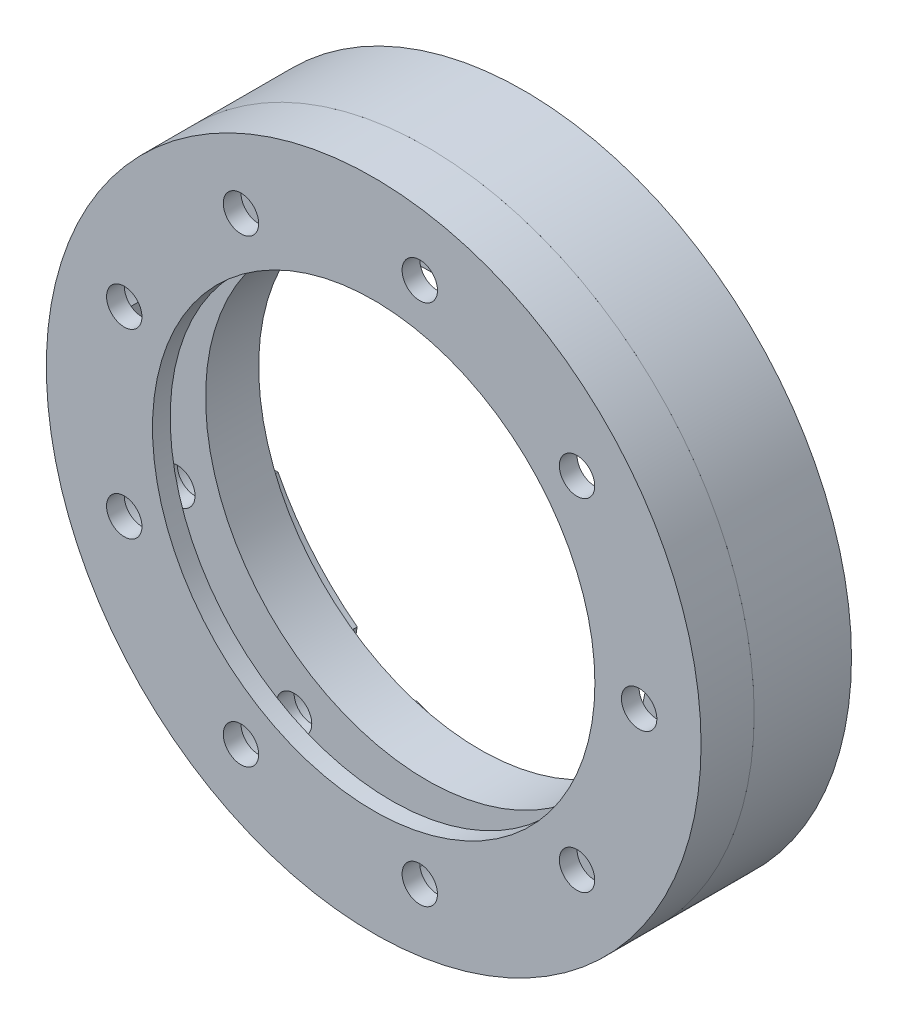
SolidWorks part; units mm, degrees
ref_plane "Front Plane" through (0, 0, 0) normal (0, 0, 1) x (1, 0, 0)
ref_plane "Top Plane" through (0, 0, 0) normal (0, 1, 0) x (1, 0, 0)
ref_plane "Right Plane" through (0, 0, 0) normal (1, 0, 0) x (0, 0, -1)
curve "Curve1"
  spline degree 3 poles (24.0011, -0.2082, 0) (23.9995, 0, 0) (24.0011, 0.2082, 0) (24.0058, 0.4158, 0) (24.0136, 0.6224, 0) (24.0244, 0.8273, 0) (24.0379, 1.0301, 0) (24.054, 1.2304, 0) (24.0724, 1.4279, 0) (24.0929, 1.6222, 0) (24.1152, 1.8132, 0) (24.139, 2.0007, 0) (24.164, 2.1846, 0) (24.1901, 2.365, 0) (24.2169, 2.5417, 0) (24.2442, 2.715, 0) (24.2718, 2.885, 0) (24.2995, 3.0517, 0) (24.3271, 3.2155, 0) (24.3545, 3.3765, 0) (24.3815, 3.5349, 0) (24.4081, 3.6909, 0) (24.4339, 3.8448, 0) (24.4591, 3.9969, 0) (24.4834, 4.1473, 0) (24.5068, 4.2962, 0) (24.5292, 4.4439, 0) (24.5506, 4.5906, 0) (24.5707, 4.7365, 0) (24.5897, 4.8817, 0) (24.6073, 5.0265, 0) (24.6236, 5.1709, 0) (24.6384, 5.3151, 0) (24.6518, 5.4593, 0) (24.6635, 5.6035, 0) (24.6736, 5.7478, 0) (24.682, 5.8924, 0) (24.6886, 6.0373, 0) (24.6934, 6.1825, 0) (24.6962, 6.3281, 0) (24.697, 6.4741, 0) (24.6958, 6.6206, 0) (24.6924, 6.7676, 0) (24.6868, 6.915, 0) (24.679, 7.0628, 0) (24.6689, 7.2111, 0) (24.6564, 7.3598, 0) (24.6415, 7.5089, 0) (24.6241, 7.6582, 0) (24.6042, 7.8078, 0) (24.5817, 7.9576, 0) (24.5566, 8.1075, 0) (24.529, 8.2575, 0) (24.4986, 8.4075, 0) (24.4656, 8.5574, 0) (24.4299, 8.7071, 0) (24.3915, 8.8565, 0) (24.3504, 9.0055, 0) (24.3065, 9.1541, 0) (24.26, 9.3022, 0) (24.2108, 9.4496, 0) (24.1589, 9.5962, 0) (24.1043, 9.742, 0) (24.0471, 9.8869, 0) (23.9874, 10.0307, 0) (23.925, 10.1735, 0) (23.8602, 10.315, 0) (23.7929, 10.4552, 0) (23.7232, 10.5941, 0) (23.6511, 10.7315, 0) (23.5768, 10.8673, 0) (23.5002, 11.0016, 0) (23.4214, 11.1342, 0) (23.3406, 11.2651, 0) (23.2577, 11.3942, 0) (23.1728, 11.5214, 0) (23.0861, 11.6468, 0) (22.9976, 11.7704, 0) (22.9073, 11.8919, 0) (22.8154, 12.0115, 0) (22.7219, 12.1292, 0) (22.6269, 12.2449, 0) (22.5304, 12.3586, 0) (22.4326, 12.4704, 0) (22.3334, 12.5802, 0) (22.2329, 12.6881, 0) (22.1313, 12.7942, 0) (22.0284, 12.8984, 0) (21.9244, 13.0009, 0) (21.8193, 13.1017, 0) (21.7131, 13.2008, 0) (21.6059, 13.2984, 0) (21.4976, 13.3945, 0) (21.3883, 13.4893, 0) (21.2779, 13.5828, 0) (21.1664, 13.6751, 0) (21.0538, 13.7665, 0) (20.94, 13.857, 0) (20.825, 13.9468, 0) (20.7087, 14.036, 0) (20.5912, 14.1249, 0) (20.4722, 14.2135, 0) (20.3517, 14.3021, 0) (20.2296, 14.3909, 0) (20.1058, 14.4801, 0) (19.9803, 14.57, 0) (19.8529, 14.6606, 0) (19.7236, 14.7524, 0) (19.5922, 14.8454, 0) (19.4588, 14.9401, 0) (19.3232, 15.0366, 0) (19.1854, 15.1352, 0) (19.0454, 15.2362, 0) (18.9033, 15.3397, 0) (18.7591, 15.4462, 0) (18.613, 15.5556, 0) (18.465, 15.6684, 0) (18.3154, 15.7846, 0) (18.1644, 15.9043, 0) (18.0124, 16.0277, 0) (17.8597, 16.1548, 0) (17.7066, 16.2855, 0) (17.5537, 16.4198, 0) (17.4013, 16.5575, 0) (17.2498, 16.6984, 0) (17.0999, 16.8422, 0) (16.9518, 16.9886, 0) (16.806, 17.1372, 0) (16.6629, 17.2876, 0) (16.5228, 17.4393, 0) (16.3859, 17.5919, 0) (16.2525, 17.7449, 0) (16.1227, 17.8979, 0) (15.9965, 18.0505, 0) (15.8741, 18.2023, 0) (15.7552, 18.3529, 0) (15.6399, 18.5021, 0) (15.528, 18.6497, 0) (15.4193, 18.7954, 0) (15.3136, 18.939, 0) (15.2107, 19.0806, 0) (15.1103, 19.22, 0) (15.0123, 19.3573, 0) (14.9163, 19.4924, 0) (14.822, 19.6253, 0) (14.7293, 19.7561, 0) (14.6379, 19.885, 0) (14.5474, 20.0119, 0) (14.4578, 20.1369, 0) (14.3687, 20.2603, 0) (14.28, 20.3819, 0) (14.1914, 20.5021, 0) (14.1027, 20.6207, 0) (14.0138, 20.7379, 0) (13.9244, 20.8539, 0) (13.8345, 20.9685, 0) (13.7437, 21.082, 0) (13.6521, 21.1944, 0) (13.5595, 21.3056, 0) (13.4657, 21.4157, 0) (13.3706, 21.5248, 0) (13.2741, 21.6328, 0) (13.1762, 21.7398, 0) (13.0766, 21.8457, 0) (12.9755, 21.9505, 0) (12.8725, 22.0542, 0) (12.7679, 22.1568, 0) (12.6613, 22.2582, 0) (12.5529, 22.3583, 0) (12.4426, 22.4572, 0) (12.3303, 22.5547, 0) (12.2161, 22.6508, 0) (12.1, 22.7455, 0) (11.9818, 22.8386, 0) (11.8617, 22.9301, 0) (11.7396, 23.0199, 0) (11.6157, 23.108, 0) (11.4898, 23.1942, 0) (11.3621, 23.2786, 0) (11.2325, 23.361, 0) (11.1012, 23.4413, 0) (10.9682, 23.5195, 0) (10.8335, 23.5956, 0) (10.6973, 23.6694, 0) (10.5595, 23.7408, 0) (10.4203, 23.81, 0) (10.2797, 23.8766, 0) (10.1379, 23.9409, 0) (9.9949, 24.0025, 0) (9.8508, 24.0617, 0) (9.7056, 24.1182, 0) (9.5596, 24.1721, 0) (9.4128, 24.2233, 0) (9.2652, 24.2719, 0) (9.117, 24.3177, 0) (8.9683, 24.3609, 0) (8.8192, 24.4013, 0) (8.6697, 24.4391, 0) (8.5199, 24.4741, 0) (8.37, 24.5064, 0) (8.22, 24.5361, 0) (8.07, 24.5632, 0) (7.9201, 24.5876, 0) (7.7704, 24.6094, 0) (7.6208, 24.6287, 0) (7.4716, 24.6454, 0) (7.3226, 24.6597, 0) (7.174, 24.6716, 0) (7.0258, 24.6812, 0) (6.8781, 24.6884, 0) (6.7308, 24.6934, 0) (6.584, 24.6963, 0) (6.4376, 24.697, 0) (6.2917, 24.6957, 0) (6.1461, 24.6924, 0) (6.001, 24.6871, 0) (5.8562, 24.6801, 0) (5.7117, 24.6713, 0) (5.5674, 24.6607, 0) (5.4232, 24.6486, 0) (5.2791, 24.6349, 0) (5.1348, 24.6197, 0) (4.9903, 24.603, 0) (4.8455, 24.585, 0) (4.7001, 24.5658, 0) (4.554, 24.5453, 0) (4.4071, 24.5237, 0) (4.2591, 24.5011, 0) (4.1098, 24.4774, 0) (3.959, 24.4529, 0) (3.8065, 24.4275, 0) (3.6521, 24.4015, 0) (3.4955, 24.3748, 0) (3.3365, 24.3477, 0) (3.1748, 24.3202, 0) (3.0103, 24.2926, 0) (2.8428, 24.2649, 0) (2.672, 24.2373, 0) (2.4979, 24.2101, 0) (2.3202, 24.1835, 0) (2.139, 24.1577, 0) (1.9542, 24.1329, 0) (1.7658, 24.1095, 0) (1.574, 24.0876, 0) (1.3788, 24.0676, 0) (1.1806, 24.0498, 0) (0.9796, 24.0343, 0) (0.7762, 24.0214, 0) (0.5709, 24.0114, 0) (0.364, 24.0043, 0) (0.1562, 24.0004, 0) (-0.0521, 23.9996, 0) (-0.2602, 24.0019, 0) (-0.4676, 24.0075, 0) (-0.6737, 24.016, 0) (-0.8782, 24.0275, 0) (-1.0804, 24.0417, 0) (-1.2801, 24.0584, 0) (-1.4768, 24.0774, 0) (-1.6703, 24.0983, 0) (-1.8604, 24.121, 0) (-2.047, 24.1451, 0) (-2.2301, 24.1705, 0) (-2.4095, 24.1967, 0) (-2.5854, 24.2237, 0) (-2.7578, 24.2511, 0) (-2.927, 24.2787, 0) (-3.093, 24.3064, 0) (-3.256, 24.334, 0) (-3.4163, 24.3613, 0) (-3.5741, 24.3882, 0) (-3.7296, 24.4146, 0) (-3.883, 24.4403, 0) (-4.0346, 24.4652, 0) (-4.1846, 24.4894, 0) (-4.3332, 24.5125, 0) (-4.4807, 24.5347, 0) (-4.6272, 24.5557, 0) (-4.7729, 24.5756, 0) (-4.918, 24.5942, 0) (-5.0626, 24.6115, 0) (-5.207, 24.6274, 0) (-5.3512, 24.6419, 0) (-5.4953, 24.6549, 0) (-5.6396, 24.6662, 0) (-5.7839, 24.6759, 0) (-5.9286, 24.6838, 0) (-6.0735, 24.69, 0) (-6.2188, 24.6943, 0) (-6.3646, 24.6966, 0) (-6.5107, 24.6969, 0) (-6.6573, 24.6951, 0) (-6.8044, 24.6912, 0) (-6.9519, 24.6851, 0) (-7.0999, 24.6767, 0) (-7.2483, 24.666, 0) (-7.397, 24.6529, 0) (-7.5462, 24.6373, 0) (-7.6956, 24.6193, 0) (-7.8452, 24.5988, 0) (-7.9951, 24.5757, 0) (-8.145, 24.55, 0) (-8.295, 24.5216, 0) (-8.445, 24.4906, 0) (-8.5948, 24.4569, 0) (-8.7444, 24.4205, 0) (-8.8938, 24.3815, 0) (-9.0427, 24.3397, 0) (-9.1912, 24.2952, 0) (-9.3391, 24.2479, 0) (-9.4863, 24.198, 0) (-9.6327, 24.1455, 0) (-9.7783, 24.0903, 0) (-9.9229, 24.0324, 0) (-10.0665, 23.972, 0) (-10.209, 23.9091, 0) (-10.3502, 23.8436, 0) (-10.4901, 23.7757, 0) (-10.6286, 23.7054, 0) (-10.7656, 23.6327, 0) (-10.9011, 23.5578, 0) (-11.0349, 23.4807, 0) (-11.1671, 23.4014, 0) (-11.2975, 23.32, 0) (-11.4262, 23.2366, 0) (-11.553, 23.1513, 0) (-11.6779, 23.0642, 0) (-11.8009, 22.9752, 0) (-11.922, 22.8845, 0) (-12.0411, 22.7922, 0) (-12.1583, 22.6983, 0) (-12.2735, 22.6029, 0) (-12.3867, 22.5061, 0) (-12.498, 22.4079, 0) (-12.6074, 22.3084, 0) (-12.7148, 22.2076, 0) (-12.8204, 22.1056, 0) (-12.9242, 22.0025, 0) (-13.0263, 21.8982, 0) (-13.1266, 21.7929, 0) (-13.2253, 21.6864, 0) (-13.3225, 21.5789, 0) (-13.4183, 21.4704, 0) (-13.5127, 21.3608, 0) (-13.606, 21.2501, 0) (-13.6981, 21.1383, 0) (-13.7892, 21.0254, 0) (-13.8795, 20.9113, 0) (-13.9692, 20.7961, 0) (-14.0583, 20.6795, 0) (-14.1471, 20.5615, 0) (-14.2357, 20.4422, 0) (-14.3243, 20.3213, 0) (-14.4132, 20.1988, 0) (-14.5025, 20.0746, 0) (-14.5925, 19.9487, 0) (-14.6834, 19.8208, 0) (-14.7755, 19.691, 0) (-14.8689, 19.5591, 0) (-14.964, 19.4251, 0) (-15.061, 19.2889, 0) (-15.1602, 19.1506, 0) (-15.2618, 19.0101, 0) (-15.3661, 18.8675, 0) (-15.4732, 18.7228, 0) (-15.5835, 18.5761, 0) (-15.6971, 18.4277, 0) (-15.8142, 18.2778, 0) (-15.9348, 18.1265, 0) (-16.0591, 17.9743, 0) (-16.1871, 17.8214, 0) (-16.3188, 17.6684, 0) (-16.4539, 17.5155, 0) (-16.5925, 17.3633, 0) (-16.7341, 17.2122, 0) (-16.8786, 17.0627, 0) (-17.0256, 16.9151, 0) (-17.1747, 16.77, 0) (-17.3254, 16.6276, 0) (-17.4774, 16.4883, 0) (-17.6301, 16.3522, 0) (-17.7832, 16.2197, 0) (-17.9361, 16.0908, 0) (-18.0885, 15.9656, 0) (-18.24, 15.844, 0) (-18.3904, 15.7261, 0) (-18.5392, 15.6116, 0) (-18.6863, 15.5005, 0) (-18.8315, 15.3926, 0) (-18.9746, 15.2876, 0) (-19.1157, 15.1854, 0) (-19.2546, 15.0856, 0) (-19.3913, 14.9881, 0) (-19.5258, 14.8926, 0) (-19.6582, 14.7987, 0) (-19.7885, 14.7063, 0) (-19.9169, 14.6152, 0) (-20.0433, 14.525, 0) (-20.1679, 14.4355, 0) (-20.2908, 14.3465, 0) (-20.4121, 14.2578, 0) (-20.5318, 14.1692, 0) (-20.6501, 14.0805, 0) (-20.767, 13.9915, 0) (-20.8826, 13.902, 0) (-20.997, 13.8119, 0) (-21.1102, 13.7209, 0) (-21.2223, 13.6291, 0) (-21.3332, 13.5362, 0) (-21.4431, 13.4421, 0) (-21.5519, 13.3466, 0) (-21.6597, 13.2498, 0) (-21.7664, 13.1514, 0) (-21.872, 13.0515, 0) (-21.9765, 12.9499, 0) (-22.08, 12.8465, 0) (-22.1822, 12.7414, 0) (-22.2833, 12.6344, 0) (-22.3831, 12.5255, 0) (-22.4817, 12.4147, 0) (-22.5789, 12.302, 0) (-22.6746, 12.1873, 0) (-22.7689, 12.0706, 0) (-22.8616, 11.952, 0) (-22.9527, 11.8314, 0) (-23.0421, 11.7088, 0) (-23.1297, 11.5844, 0) (-23.2155, 11.458, 0) (-23.2994, 11.3299, 0) (-23.3812, 11.1999, 0) (-23.461, 11.0681, 0) (-23.5387, 10.9347, 0) (-23.6142, 10.7996, 0) (-23.6874, 10.663, 0) (-23.7583, 10.5248, 0) (-23.8268, 10.3853, 0) (-23.8929, 10.2444, 0) (-23.9565, 10.1022, 0) (-24.0176, 9.9589, 0) (-24.076, 9.8146, 0) (-24.1319, 9.6692, 0) (-24.1851, 9.523, 0) (-24.2357, 9.3759, 0) (-24.2836, 9.2282, 0) (-24.3288, 9.0799, 0) (-24.3713, 8.9311, 0) (-24.411, 8.7818, 0) (-24.4481, 8.6322, 0) (-24.4824, 8.4825, 0) (-24.5141, 8.3325, 0) (-24.5431, 8.1825, 0) (-24.5695, 8.0326, 0) (-24.5933, 7.8827, 0) (-24.6144, 7.733, 0) (-24.6331, 7.5835, 0) (-24.6492, 7.4343, 0) (-24.6629, 7.2854, 0) (-24.6742, 7.1369, 0) (-24.6832, 6.9889, 0) (-24.6899, 6.8412, 0) (-24.6943, 6.6941, 0) (-24.6966, 6.5473, 0) (-24.6968, 6.4011, 0) (-24.695, 6.2552, 0) (-24.6912, 6.1098, 0) (-24.6855, 5.9648, 0) (-24.678, 5.8201, 0) (-24.6688, 5.6756, 0) (-24.6579, 5.5314, 0) (-24.6453, 5.3872, 0) (-24.6312, 5.243, 0) (-24.6156, 5.0987, 0) (-24.5987, 4.9542, 0) (-24.5804, 4.8092, 0) (-24.5608, 4.6637, 0) (-24.54, 4.5174, 0) (-24.5182, 4.3702, 0) (-24.4952, 4.2219, 0) (-24.4714, 4.0723, 0) (-24.4466, 3.9211, 0) (-24.4211, 3.7681, 0) (-24.3949, 3.6132, 0) (-24.3681, 3.456, 0) (-24.3409, 3.2963, 0) (-24.3133, 3.134, 0) (-24.2857, 2.9687, 0) (-24.258, 2.8004, 0) (-24.2305, 2.6288, 0) (-24.2034, 2.4538, 0) (-24.177, 2.2752, 0) (-24.1514, 2.0931, 0) (-24.1269, 1.9074, 0) (-24.1038, 1.7182, 0) (-24.0824, 1.5255, 0) (-24.0629, 1.3295, 0) (-24.0457, 1.1306, 0) (-24.0308, 0.929, 0) (-24.0187, 0.725, 0) (-24.0093, 0.5193, 0) (-24.003, 0.3121, 0) (-23.9999, 0.1041, 0) (-23.9999, -0.1041, 0) (-24.003, -0.3121, 0) (-24.0093, -0.5193, 0) (-24.0187, -0.725, 0) (-24.0308, -0.929, 0) (-24.0457, -1.1306, 0) (-24.0629, -1.3295, 0) (-24.0824, -1.5255, 0) (-24.1038, -1.7182, 0) (-24.1269, -1.9074, 0) (-24.1514, -2.0931, 0) (-24.177, -2.2752, 0) (-24.2034, -2.4538, 0) (-24.2305, -2.6288, 0) (-24.258, -2.8004, 0) (-24.2857, -2.9687, 0) (-24.3133, -3.134, 0) (-24.3409, -3.2963, 0) (-24.3681, -3.456, 0) (-24.3949, -3.6132, 0) (-24.4211, -3.7681, 0) (-24.4466, -3.9211, 0) (-24.4714, -4.0723, 0) (-24.4952, -4.2219, 0) (-24.5182, -4.3702, 0) (-24.54, -4.5174, 0) (-24.5608, -4.6637, 0) (-24.5804, -4.8092, 0) (-24.5987, -4.9542, 0) (-24.6156, -5.0987, 0) (-24.6312, -5.243, 0) (-24.6453, -5.3872, 0) (-24.6579, -5.5314, 0) (-24.6688, -5.6756, 0) (-24.678, -5.8201, 0) (-24.6855, -5.9648, 0) (-24.6912, -6.1098, 0) (-24.695, -6.2552, 0) (-24.6968, -6.4011, 0) (-24.6966, -6.5473, 0) (-24.6943, -6.6941, 0) (-24.6899, -6.8412, 0) (-24.6832, -6.9889, 0) (-24.6742, -7.1369, 0) (-24.6629, -7.2854, 0) (-24.6492, -7.4343, 0) (-24.6331, -7.5835, 0) (-24.6144, -7.733, 0) (-24.5933, -7.8827, 0) (-24.5695, -8.0326, 0) (-24.5431, -8.1825, 0) (-24.5141, -8.3325, 0) (-24.4824, -8.4825, 0) (-24.4481, -8.6322, 0) (-24.411, -8.7818, 0) (-24.3713, -8.9311, 0) (-24.3288, -9.0799, 0) (-24.2836, -9.2282, 0) (-24.2357, -9.3759, 0) (-24.1851, -9.523, 0) (-24.1319, -9.6692, 0) (-24.076, -9.8146, 0) (-24.0176, -9.9589, 0) (-23.9565, -10.1022, 0) (-23.8929, -10.2444, 0) (-23.8268, -10.3853, 0) (-23.7583, -10.5248, 0) (-23.6874, -10.663, 0) (-23.6142, -10.7996, 0) (-23.5387, -10.9347, 0) (-23.461, -11.0681, 0) (-23.3812, -11.1999, 0) (-23.2994, -11.3299, 0) (-23.2155, -11.458, 0) (-23.1297, -11.5844, 0) (-23.0421, -11.7088, 0) (-22.9527, -11.8314, 0) (-22.8616, -11.952, 0) (-22.7689, -12.0706, 0) (-22.6746, -12.1873, 0) (-22.5789, -12.302, 0) (-22.4817, -12.4147, 0) (-22.3831, -12.5255, 0) (-22.2833, -12.6344, 0) (-22.1822, -12.7414, 0) (-22.08, -12.8465, 0) (-21.9765, -12.9499, 0) (-21.872, -13.0515, 0) (-21.7664, -13.1514, 0) (-21.6597, -13.2498, 0) (-21.5519, -13.3466, 0) (-21.4431, -13.4421, 0) (-21.3332, -13.5362, 0) (-21.2223, -13.6291, 0) (-21.1102, -13.7209, 0) (-20.997, -13.8119, 0) (-20.8826, -13.902, 0) (-20.767, -13.9915, 0) (-20.6501, -14.0805, 0) (-20.5318, -14.1692, 0) (-20.4121, -14.2578, 0) (-20.2908, -14.3465, 0) (-20.1679, -14.4355, 0) (-20.0433, -14.525, 0) (-19.9169, -14.6152, 0) (-19.7885, -14.7063, 0) (-19.6582, -14.7987, 0) (-19.5258, -14.8926, 0) (-19.3913, -14.9881, 0) (-19.2546, -15.0856, 0) (-19.1157, -15.1854, 0) (-18.9746, -15.2876, 0) (-18.8315, -15.3926, 0) (-18.6863, -15.5005, 0) (-18.5392, -15.6116, 0) (-18.3904, -15.7261, 0) (-18.24, -15.844, 0) (-18.0885, -15.9656, 0) (-17.9361, -16.0908, 0) (-17.7832, -16.2197, 0) (-17.6301, -16.3522, 0) (-17.4774, -16.4883, 0) (-17.3254, -16.6276, 0) (-17.1747, -16.77, 0) (-17.0256, -16.9151, 0) (-16.8786, -17.0627, 0) (-16.7341, -17.2122, 0) (-16.5925, -17.3633, 0) (-16.4539, -17.5155, 0) (-16.3188, -17.6684, 0) (-16.1871, -17.8214, 0) (-16.0591, -17.9743, 0) (-15.9348, -18.1265, 0) (-15.8142, -18.2778, 0) (-15.6971, -18.4277, 0) (-15.5835, -18.5761, 0) (-15.4732, -18.7228, 0) (-15.3661, -18.8675, 0) (-15.2618, -19.0101, 0) (-15.1602, -19.1506, 0) (-15.061, -19.2889, 0) (-14.964, -19.4251, 0) (-14.8689, -19.5591, 0) (-14.7755, -19.691, 0) (-14.6834, -19.8208, 0) (-14.5925, -19.9487, 0) (-14.5025, -20.0746, 0) (-14.4132, -20.1988, 0) (-14.3243, -20.3213, 0) (-14.2357, -20.4422, 0) (-14.1471, -20.5615, 0) (-14.0583, -20.6795, 0) (-13.9692, -20.7961, 0) (-13.8795, -20.9113, 0) (-13.7892, -21.0254, 0) (-13.6981, -21.1383, 0) (-13.606, -21.2501, 0) (-13.5127, -21.3608, 0) (-13.4183, -21.4704, 0) (-13.3225, -21.5789, 0) (-13.2253, -21.6864, 0) (-13.1266, -21.7929, 0) (-13.0263, -21.8982, 0) (-12.9242, -22.0025, 0) (-12.8204, -22.1056, 0) (-12.7148, -22.2076, 0) (-12.6074, -22.3084, 0) (-12.498, -22.4079, 0) (-12.3867, -22.5061, 0) (-12.2735, -22.6029, 0) (-12.1583, -22.6983, 0) (-12.0411, -22.7922, 0) (-11.922, -22.8845, 0) (-11.8009, -22.9752, 0) (-11.6779, -23.0642, 0) (-11.553, -23.1513, 0) (-11.4262, -23.2366, 0) (-11.2975, -23.32, 0) (-11.1671, -23.4014, 0) (-11.0349, -23.4807, 0) (-10.9011, -23.5578, 0) (-10.7656, -23.6327, 0) (-10.6286, -23.7054, 0) (-10.4901, -23.7757, 0) (-10.3502, -23.8436, 0) (-10.209, -23.9091, 0) (-10.0665, -23.972, 0) (-9.9229, -24.0324, 0) (-9.7783, -24.0903, 0) (-9.6327, -24.1455, 0) (-9.4863, -24.198, 0) (-9.3391, -24.2479, 0) (-9.1912, -24.2952, 0) (-9.0427, -24.3397, 0) (-8.8938, -24.3815, 0) (-8.7444, -24.4205, 0) (-8.5948, -24.4569, 0) (-8.445, -24.4906, 0) (-8.295, -24.5216, 0) (-8.145, -24.55, 0) (-7.9951, -24.5757, 0) (-7.8452, -24.5988, 0) (-7.6956, -24.6193, 0) (-7.5462, -24.6373, 0) (-7.397, -24.6529, 0) (-7.2483, -24.666, 0) (-7.0999, -24.6767, 0) (-6.9519, -24.6851, 0) (-6.8044, -24.6912, 0) (-6.6573, -24.6951, 0) (-6.5107, -24.6969, 0) (-6.3646, -24.6966, 0) (-6.2188, -24.6943, 0) (-6.0735, -24.69, 0) (-5.9286, -24.6838, 0) (-5.7839, -24.6759, 0) (-5.6396, -24.6662, 0) (-5.4953, -24.6549, 0) (-5.3512, -24.6419, 0) (-5.207, -24.6274, 0) (-5.0626, -24.6115, 0) (-4.918, -24.5942, 0) (-4.7729, -24.5756, 0) (-4.6272, -24.5557, 0) (-4.4807, -24.5347, 0) (-4.3332, -24.5125, 0) (-4.1846, -24.4894, 0) (-4.0346, -24.4652, 0) (-3.883, -24.4403, 0) (-3.7296, -24.4146, 0) (-3.5741, -24.3882, 0) (-3.4163, -24.3613, 0) (-3.256, -24.334, 0) (-3.093, -24.3064, 0) (-2.927, -24.2787, 0) (-2.7578, -24.2511, 0) (-2.5854, -24.2237, 0) (-2.4095, -24.1967, 0) (-2.2301, -24.1705, 0) (-2.047, -24.1451, 0) (-1.8604, -24.121, 0) (-1.6703, -24.0983, 0) (-1.4768, -24.0774, 0) (-1.2801, -24.0584, 0) (-1.0804, -24.0417, 0) (-0.8782, -24.0275, 0) (-0.6737, -24.016, 0) (-0.4676, -24.0075, 0) (-0.2602, -24.0019, 0) (-0.0521, -23.9996, 0) (0.1562, -24.0004, 0) (0.364, -24.0043, 0) (0.5709, -24.0114, 0) (0.7762, -24.0214, 0) (0.9796, -24.0343, 0) (1.1806, -24.0498, 0) (1.3788, -24.0676, 0) (1.574, -24.0876, 0) (1.7658, -24.1095, 0) (1.9542, -24.1329, 0) (2.139, -24.1577, 0) (2.3202, -24.1835, 0) (2.4979, -24.2101, 0) (2.672, -24.2373, 0) (2.8428, -24.2649, 0) (3.0103, -24.2926, 0) (3.1748, -24.3202, 0) (3.3365, -24.3477, 0) (3.4955, -24.3748, 0) (3.6521, -24.4015, 0) (3.8065, -24.4275, 0) (3.959, -24.4529, 0) (4.1098, -24.4774, 0) (4.2591, -24.5011, 0) (4.4071, -24.5237, 0) (4.554, -24.5453, 0) (4.7001, -24.5658, 0) (4.8455, -24.585, 0) (4.9903, -24.603, 0) (5.1348, -24.6197, 0) (5.2791, -24.6349, 0) (5.4232, -24.6486, 0) (5.5674, -24.6607, 0) (5.7117, -24.6713, 0) (5.8562, -24.6801, 0) (6.001, -24.6871, 0) (6.1461, -24.6924, 0) (6.2917, -24.6957, 0) (6.4376, -24.697, 0) (6.584, -24.6963, 0) (6.7308, -24.6934, 0) (6.8781, -24.6884, 0) (7.0258, -24.6812, 0) (7.174, -24.6716, 0) (7.3226, -24.6597, 0) (7.4716, -24.6454, 0) (7.6208, -24.6287, 0) (7.7704, -24.6094, 0) (7.9201, -24.5876, 0) (8.07, -24.5632, 0) (8.22, -24.5361, 0) (8.37, -24.5064, 0) (8.5199, -24.4741, 0) (8.6697, -24.4391, 0) (8.8192, -24.4013, 0) (8.9683, -24.3609, 0) (9.117, -24.3177, 0) (9.2652, -24.2719, 0) (9.4128, -24.2233, 0) (9.5596, -24.1721, 0) (9.7056, -24.1182, 0) (9.8508, -24.0617, 0) (9.9949, -24.0025, 0) (10.1379, -23.9409, 0) (10.2797, -23.8766, 0) (10.4203, -23.81, 0) (10.5595, -23.7408, 0) (10.6973, -23.6694, 0) (10.8335, -23.5956, 0) (10.9682, -23.5195, 0) (11.1012, -23.4413, 0) (11.2325, -23.361, 0) (11.3621, -23.2786, 0) (11.4898, -23.1942, 0) (11.6157, -23.108, 0) (11.7396, -23.0199, 0) (11.8617, -22.9301, 0) (11.9818, -22.8386, 0) (12.1, -22.7455, 0) (12.2161, -22.6508, 0) (12.3303, -22.5547, 0) (12.4426, -22.4572, 0) (12.5529, -22.3583, 0) (12.6613, -22.2582, 0) (12.7679, -22.1568, 0) (12.8725, -22.0542, 0) (12.9755, -21.9505, 0) (13.0766, -21.8457, 0) (13.1762, -21.7398, 0) (13.2741, -21.6328, 0) (13.3706, -21.5248, 0) (13.4657, -21.4157, 0) (13.5595, -21.3056, 0) (13.6521, -21.1944, 0) (13.7437, -21.082, 0) (13.8345, -20.9685, 0) (13.9244, -20.8539, 0) (14.0138, -20.7379, 0) (14.1027, -20.6207, 0) (14.1914, -20.5021, 0) (14.28, -20.3819, 0) (14.3687, -20.2603, 0) (14.4578, -20.1369, 0) (14.5474, -20.0119, 0) (14.6379, -19.885, 0) (14.7293, -19.7561, 0) (14.822, -19.6253, 0) (14.9163, -19.4924, 0) (15.0123, -19.3573, 0) (15.1103, -19.22, 0) (15.2107, -19.0806, 0) (15.3136, -18.939, 0) (15.4193, -18.7954, 0) (15.528, -18.6497, 0) (15.6399, -18.5021, 0) (15.7552, -18.3529, 0) (15.8741, -18.2023, 0) (15.9965, -18.0505, 0) (16.1227, -17.8979, 0) (16.2525, -17.7449, 0) (16.3859, -17.5919, 0) (16.5228, -17.4393, 0) (16.6629, -17.2876, 0) (16.806, -17.1372, 0) (16.9518, -16.9886, 0) (17.0999, -16.8422, 0) (17.2498, -16.6984, 0) (17.4013, -16.5575, 0) (17.5537, -16.4198, 0) (17.7066, -16.2855, 0) (17.8597, -16.1548, 0) (18.0124, -16.0277, 0) (18.1644, -15.9043, 0) (18.3154, -15.7846, 0) (18.465, -15.6684, 0) (18.613, -15.5556, 0) (18.7591, -15.4462, 0) (18.9033, -15.3397, 0) (19.0454, -15.2362, 0) (19.1854, -15.1352, 0) (19.3232, -15.0366, 0) (19.4588, -14.9401, 0) (19.5922, -14.8454, 0) (19.7236, -14.7524, 0) (19.8529, -14.6606, 0) (19.9803, -14.57, 0) (20.1058, -14.4801, 0) (20.2296, -14.3909, 0) (20.3517, -14.3021, 0) (20.4722, -14.2135, 0) (20.5912, -14.1249, 0) (20.7087, -14.036, 0) (20.825, -13.9468, 0) (20.94, -13.857, 0) (21.0538, -13.7665, 0) (21.1664, -13.6751, 0) (21.2779, -13.5828, 0) (21.3883, -13.4893, 0) (21.4976, -13.3945, 0) (21.6059, -13.2984, 0) (21.7131, -13.2008, 0) (21.8193, -13.1017, 0) (21.9244, -13.0009, 0) (22.0284, -12.8984, 0) (22.1313, -12.7942, 0) (22.2329, -12.6881, 0) (22.3334, -12.5802, 0) (22.4326, -12.4704, 0) (22.5304, -12.3586, 0) (22.6269, -12.2449, 0) (22.7219, -12.1292, 0) (22.8154, -12.0115, 0) (22.9073, -11.8919, 0) (22.9976, -11.7704, 0) (23.0861, -11.6468, 0) (23.1728, -11.5214, 0) (23.2577, -11.3942, 0) (23.3406, -11.2651, 0) (23.4214, -11.1342, 0) (23.5002, -11.0016, 0) (23.5768, -10.8673, 0) (23.6511, -10.7315, 0) (23.7232, -10.5941, 0) (23.7929, -10.4552, 0) (23.8602, -10.315, 0) (23.925, -10.1735, 0) (23.9874, -10.0307, 0) (24.0471, -9.8869, 0) (24.1043, -9.742, 0) (24.1589, -9.5962, 0) (24.2108, -9.4496, 0) (24.26, -9.3022, 0) (24.3065, -9.1541, 0) (24.3504, -9.0055, 0) (24.3915, -8.8565, 0) (24.4299, -8.7071, 0) (24.4656, -8.5574, 0) (24.4986, -8.4075, 0) (24.529, -8.2575, 0) (24.5566, -8.1075, 0) (24.5817, -7.9576, 0) (24.6042, -7.8078, 0) (24.6241, -7.6582, 0) (24.6415, -7.5089, 0) (24.6564, -7.3598, 0) (24.6689, -7.2111, 0) (24.679, -7.0628, 0) (24.6868, -6.915, 0) (24.6924, -6.7676, 0) (24.6958, -6.6206, 0) (24.697, -6.4741, 0) (24.6962, -6.3281, 0) (24.6934, -6.1825, 0) (24.6886, -6.0373, 0) (24.682, -5.8924, 0) (24.6736, -5.7478, 0) (24.6635, -5.6035, 0) (24.6518, -5.4593, 0) (24.6384, -5.3151, 0) (24.6236, -5.1709, 0) (24.6073, -5.0265, 0) (24.5897, -4.8817, 0) (24.5707, -4.7365, 0) (24.5506, -4.5906, 0) (24.5292, -4.4439, 0) (24.5068, -4.2962, 0) (24.4834, -4.1473, 0) (24.4591, -3.9969, 0) (24.4339, -3.8448, 0) (24.4081, -3.6909, 0) (24.3815, -3.5349, 0) (24.3545, -3.3765, 0) (24.3271, -3.2155, 0) (24.2995, -3.0517, 0) (24.2718, -2.885, 0) (24.2442, -2.715, 0) (24.2169, -2.5417, 0) (24.1901, -2.365, 0) (24.164, -2.1846, 0) (24.139, -2.0007, 0) (24.1152, -1.8132, 0) (24.0929, -1.6222, 0) (24.0724, -1.4279, 0) (24.054, -1.2304, 0) (24.0379, -1.0301, 0) (24.0244, -0.8273, 0) (24.0136, -0.6224, 0) (24.0058, -0.4158, 0) (24.0011, -0.2082, 0) (23.9995, 0, 0) (24.0011, 0.2082, 0) knots -0.003862 -0.00258 -0.001291 0 0.001291 0.00258 0.003862 0.005134 0.006395 0.007641 0.008871 0.010083 0.011275 0.012446 0.013597 0.014726 0.015834 0.016921 0.017988 0.019035 0.020064 0.021076 0.022071 0.023052 0.024019 0.024974 0.025917 0.026851 0.027777 0.028696 0.029608 0.030515 0.031419 0.032319 0.033217 0.034114 0.035011 0.035908 0.036805 0.037703 0.038604 0.039506 0.040411 0.041319 0.04223 0.043144 0.044062 0.044983 0.045908 0.046836 0.047768 0.048703 0.049642 0.050585 0.05153 0.052478 0.053429 0.054383 0.055339 0.056298 0.057258 0.05822 0.059183 0.060147 0.061112 0.062078 0.063043 0.064008 0.064973 0.065937 0.0669 0.067862 0.068822 0.06978 0.070736 0.07169 0.07264 0.073588 0.074533 0.075475 0.076414 0.077349 0.07828 0.079208 0.080132 0.081053 0.08197 0.082884 0.083794 0.084702 0.085607 0.086509 0.087409 0.088307 0.089205 0.090101 0.090998 0.091895 0.092793 0.093694 0.094598 0.095506 0.096419 0.097338 0.098265 0.0992 0.100145 0.101101 0.10207 0.103052 0.10405 0.105063 0.106095 0.107144 0.108214 0.109303 0.110414 0.111546 0.112699 0.113873 0.115068 0.116282 0.117514 0.118762 0.120024 0.121298 0.122581 0.12387 0.125161 0.126453 0.12774 0.129021 0.130292 0.131551 0.132796 0.134023 0.135233 0.136422 0.137591 0.138739 0.139865 0.140971 0.142055 0.14312 0.144165 0.145192 0.146201 0.147195 0.148174 0.149139 0.150092 0.151035 0.151968 0.152892 0.15381 0.154722 0.155628 0.156531 0.157431 0.15833 0.159227 0.160123 0.16102 0.161917 0.162816 0.163717 0.164619 0.165525 0.166433 0.167344 0.168259 0.169177 0.170099 0.171024 0.171953 0.172885 0.173821 0.17476 0.175703 0.176648 0.177597 0.178549 0.179503 0.180459 0.181418 0.182378 0.18334 0.184304 0.185268 0.186233 0.187198 0.188164 0.189129 0.190094 0.191058 0.192021 0.192982 0.193942 0.1949 0.195855 0.196809 0.197759 0.198707 0.199651 0.200593 0.201531 0.202465 0.203396 0.204324 0.205247 0.206168 0.207084 0.207998 0.208908 0.209815 0.210719 0.211621 0.212521 0.21342 0.214317 0.215213 0.21611 0.217007 0.217906 0.218807 0.219711 0.22062 0.221533 0.222454 0.223381 0.224318 0.225264 0.226222 0.227192 0.228176 0.229175 0.230191 0.231225 0.232277 0.233349 0.234441 0.235554 0.236689 0.237845 0.239022 0.240219 0.241435 0.242669 0.243919 0.245183 0.246458 0.247742 0.249031 0.250323 0.251614 0.252901 0.254181 0.255451 0.256708 0.25795 0.259176 0.260382 0.261569 0.262736 0.263881 0.265005 0.266108 0.26719 0.268252 0.269294 0.270319 0.271326 0.272318 0.273295 0.274259 0.275211 0.276152 0.277084 0.278007 0.278924 0.279835 0.280741 0.281644 0.282544 0.283442 0.284339 0.285235 0.286132 0.287029 0.287928 0.288829 0.289732 0.290638 0.291547 0.292458 0.293374 0.294292 0.295214 0.29614 0.297069 0.298002 0.298938 0.299878 0.300821 0.301767 0.302716 0.303668 0.304622 0.305579 0.306538 0.307498 0.308461 0.309424 0.310388 0.311354 0.312319 0.313284 0.31425 0.315214 0.316178 0.317141 0.318102 0.319062 0.320019 0.320975 0.321928 0.322878 0.323825 0.324769 0.32571 0.326648 0.327582 0.328512 0.329439 0.330363 0.331282 0.332199 0.333112 0.334021 0.334928 0.335832 0.336734 0.337634 0.338532 0.339429 0.340325 0.341222 0.342119 0.343018 0.34392 0.344825 0.345734 0.346648 0.347569 0.348498 0.349435 0.350383 0.351342 0.352314 0.3533 0.354302 0.355319 0.356355 0.35741 0.358484 0.359579 0.360695 0.361832 0.362991 0.36417 0.36537 0.366588 0.367824 0.369076 0.370342 0.371618 0.372903 0.374193 0.375484 0.376775 0.378061 0.37934 0.380608 0.381864 0.383104 0.384327 0.385532 0.386716 0.38788 0.389023 0.390144 0.391244 0.392323 0.393383 0.394423 0.395446 0.396451 0.397441 0.398416 0.399378 0.400329 0.401269 0.402199 0.403122 0.404038 0.404949 0.405854 0.406757 0.407656 0.408554 0.409451 0.410347 0.411244 0.412142 0.413041 0.413942 0.414845 0.415752 0.416661 0.417573 0.418488 0.419407 0.42033 0.421256 0.422185 0.423118 0.424055 0.424995 0.425939 0.426885 0.427835 0.428787 0.429742 0.430699 0.431658 0.432619 0.433581 0.434545 0.435509 0.436474 0.43744 0.438405 0.43937 0.440335 0.441299 0.442261 0.443222 0.444182 0.445139 0.446094 0.447047 0.447996 0.448943 0.449887 0.450828 0.451765 0.452698 0.453628 0.454555 0.455478 0.456397 0.457313 0.458226 0.459135 0.460041 0.460945 0.461847 0.462746 0.463644 0.464541 0.465437 0.466334 0.467232 0.468131 0.469033 0.469938 0.470848 0.471763 0.472685 0.473614 0.474553 0.475502 0.476463 0.477437 0.478424 0.479428 0.480448 0.481486 0.482543 0.48362 0.484718 0.485836 0.486976 0.488137 0.489319 0.490521 0.491742 0.49298 0.494234 0.495501 0.496778 0.498064 0.499354 0.500646 0.501936 0.503222 0.504499 0.505766 0.50702 0.508258 0.509479 0.510681 0.511863 0.513024 0.514164 0.515282 0.51638 0.517457 0.518514 0.519552 0.520572 0.521576 0.522563 0.523537 0.524498 0.525447 0.526386 0.527315 0.528237 0.529152 0.530062 0.530967 0.531869 0.532768 0.533666 0.534563 0.535459 0.536356 0.537254 0.538153 0.539055 0.539959 0.540865 0.541774 0.542687 0.543603 0.544522 0.545445 0.546372 0.547302 0.548235 0.549172 0.550113 0.551057 0.552004 0.552953 0.553906 0.554861 0.555818 0.556778 0.557739 0.558701 0.559665 0.56063 0.561595 0.56256 0.563526 0.564491 0.565455 0.566419 0.567381 0.568342 0.569301 0.570258 0.571213 0.572165 0.573115 0.574061 0.575005 0.575945 0.576882 0.577815 0.578744 0.57967 0.580593 0.581512 0.582427 0.583339 0.584248 0.585155 0.586058 0.586959 0.587858 0.588756 0.589653 0.590549 0.591446 0.592344 0.593243 0.594146 0.595051 0.595962 0.596878 0.597801 0.598731 0.599671 0.600622 0.601584 0.602559 0.603549 0.604554 0.605577 0.606617 0.607677 0.608756 0.609856 0.610977 0.61212 0.613284 0.614468 0.615673 0.616896 0.618136 0.619392 0.62066 0.621939 0.623225 0.624516 0.625807 0.627097 0.628382 0.629658 0.630924 0.632176 0.633412 0.63463 0.63583 0.637009 0.638168 0.639305 0.640421 0.641516 0.64259 0.643645 0.644681 0.645698 0.6467 0.647686 0.648658 0.649617 0.650565 0.651502 0.652431 0.653352 0.654266 0.655175 0.65608 0.656982 0.657881 0.658778 0.659675 0.660571 0.661468 0.662366 0.663266 0.664168 0.665072 0.665979 0.666888 0.667801 0.668718 0.669637 0.670561 0.671488 0.672418 0.673352 0.67429 0.675231 0.676175 0.677122 0.678072 0.679025 0.679981 0.680938 0.681898 0.682859 0.683822 0.684786 0.68575 0.686716 0.687681 0.688646 0.689612 0.690576 0.691539 0.692502 0.693462 0.694421 0.695378 0.696332 0.697284 0.698233 0.699179 0.700122 0.701062 0.701998 0.702931 0.70386 0.704786 0.705708 0.706626 0.707542 0.708453 0.709362 0.710268 0.711171 0.712072 0.712971 0.713868 0.714765 0.715661 0.716558 0.717456 0.718356 0.719259 0.720165 0.721076 0.721993 0.722916 0.723848 0.724789 0.725741 0.726705 0.727682 0.728674 0.729681 0.730706 0.731748 0.73281 0.733892 0.734995 0.736119 0.737264 0.738431 0.739618 0.740824 0.74205 0.743292 0.744549 0.745819 0.747099 0.748386 0.749677 0.750969 0.752258 0.753542 0.754817 0.756081 0.757331 0.758565 0.759781 0.760978 0.762155 0.763311 0.764446 0.765559 0.766651 0.767723 0.768775 0.769809 0.770825 0.771824 0.772808 0.773778 0.774736 0.775682 0.776619 0.777546 0.778467 0.77938 0.780289 0.781193 0.782094 0.782993 0.78389 0.784787 0.785683 0.78658 0.787479 0.788379 0.789281 0.790185 0.791092 0.792002 0.792916 0.793832 0.794753 0.795676 0.796604 0.797535 0.798469 0.799407 0.800349 0.801293 0.802241 0.803191 0.804145 0.8051 0.806058 0.807018 0.807979 0.808942 0.809906 0.810871 0.811836 0.812802 0.813767 0.814732 0.815696 0.81666 0.817622 0.818582 0.819541 0.820497 0.821451 0.822403 0.823352 0.824297 0.82524 0.826179 0.827115 0.828047 0.828976 0.829901 0.830823 0.831741 0.832656 0.833567 0.834475 0.835381 0.836283 0.837184 0.838083 0.83898 0.839877 0.840773 0.84167 0.842569 0.843469 0.844372 0.845278 0.84619 0.847108 0.848032 0.848965 0.849908 0.850861 0.851826 0.852805 0.853799 0.854808 0.855835 0.85688 0.857945 0.859029 0.860135 0.861261 0.862409 0.863578 0.864767 0.865977 0.867204 0.868449 0.869708 0.870979 0.87226 0.873547 0.874839 0.87613 0.877419 0.878702 0.879976 0.881238 0.882486 0.883718 0.884932 0.886127 0.887301 0.888454 0.889586 0.890697 0.891786 0.892856 0.893905 0.894937 0.89595 0.896948 0.89793 0.898899 0.899855 0.9008 0.901735 0.902662 0.903581 0.904494 0.905402 0.906306 0.907207 0.908105 0.909002 0.909899 0.910795 0.911693 0.912591 0.913491 0.914393 0.915298 0.916206 0.917116 0.91803 0.918947 0.919868 0.920792 0.92172 0.922651 0.923586 0.924525 0.925467 0.926412 0.92736 0.92831 0.929264 0.93022 0.931178 0.932138 0.9331 0.934063 0.935027 0.935992 0.936957 0.937922 0.938888 0.939853 0.940817 0.94178 0.942742 0.943702 0.944661 0.945617 0.946571 0.947522 0.94847 0.949415 0.950358 0.951297 0.952232 0.953164 0.954092 0.955017 0.955938 0.956856 0.95777 0.958681 0.959589 0.960494 0.961396 0.962297 0.963195 0.964092 0.964989 0.965886 0.966783 0.967681 0.968581 0.969485 0.970392 0.971304 0.972223 0.973149 0.974083 0.975026 0.975981 0.976948 0.977929 0.978924 0.979936 0.980965 0.982012 0.983079 0.984166 0.985274 0.986403 0.987554 0.988725 0.989917 0.991129 0.992359 0.993605 0.994866 0.996138 0.99742 0.998709 1 1.001291 1.00258 1.003862 periodic
sketch "Sketch2" plane through (0, 0, 0) normal (0, 0, 1) x (1, 0, 0)
  circle A0 centre (0, 0) radius 37
  dimension "D1" = 74
extrude "Boss-Extrude1" add sketch "Sketch2" along normal blind 6
sketch "Sketch5" plane through (0, 0, 0) normal (0, 0, 1) x (1, 0, 0)
  circle A0 centre (0, 0) radius 31.25
  circle A1 centre (0, 0) radius 37 construction
  circle A2 centre (0, 0) radius 37
  dimension "D1" = 62.5
extrude "Boss-Extrude2" add sketch "Sketch5" against normal blind 5
sketch "Sketch6" plane through (0, 0, 6) normal (0, 0, 1) x (1, 0, 0)
  circle A0 centre (0, 0) radius 25
  circle A1 centre (0, 0) radius 37 construction
  circle A2 centre (0, 0) radius 37
  dimension "D1" = 50
extrude "Boss-Extrude3" add sketch "Sketch6" along normal blind 6
sketch "Sketch7" plane through (0, 0, 0) normal (0, 0, 1) x (1, 0, 0)
  line L0 (-1000, 37) -> (49000, 37) construction
  line L1 (0, -1000) -> (0, 49000) construction
  line L2 (0, 32.3993) -> (0.6403, 32.3993)
  line L3 (0.6403, 32.3993) -> (0.6403, 33.8323)
  line L4 (0.6403, 33.8323) -> (1.8002, 33.8323)
  line L5 (1.8002, 33.8323) -> (0, 36.1112)
  line L6 (0, 36.1112) -> (-1.8002, 33.8323)
  line L7 (-1.8002, 33.8323) -> (-0.6403, 33.8323)
  line L8 (-0.6403, 33.8323) -> (-0.6403, 32.3993)
  line L9 (-0.6403, 32.3993) -> (0, 32.3993)
extrude "Cut-Extrude2" cut sketch "Sketch7" against normal through all
sketch "Sketch9" plane through (0, 0, 12) normal (0, 0, 1) x (1, 0, 0)
  circle A0 centre (30, 0) radius 2
  point P2 (0, 0)
  point P4 (0, 0)
  dimension "D1" = 4
  dimension "D2" = 30
extrude "Cut-Extrude4" cut sketch "Sketch9" against normal through all
sketch "Sketch12" plane through (0, 0, -5) normal (0, 0, -1) x (-1, 0, 0)
  circle A0 centre (-30, 0) radius 4
  dimension "D1" = 8
extrude "Cut-Extrude5" cut sketch "Sketch12" against normal offset from surface (9 mm away) 4 up to face at (-1.625, 0, 0) offset beyond the face yes
sketch "Sketch13" plane through (0, 0, 12) normal (0, 0, 1) x (1, 0, 0)
  circle A0 centre (0, 0) radius 25
  dimension "D1" = 50
extrude "Cut-Extrude6" cut sketch "Sketch13" against normal through all
sketch "Sketch15" plane through (0, 0, 4) normal (0, 0, 1) x (1, 0, 0)
  circle A0 centre (30, 0) radius 5.5
  dimension "D1" = 11
extrude "Cut-Extrude7" cut sketch "Sketch15" along normal blind 4 from offset 2
pattern_circular "CirPattern7" count 9 over 360 about axis through (0, 0, 0) along (0, 0, 1) of "Cut-Extrude5", "Cut-Extrude4", "Cut-Extrude7"
sketch "Sketch16" plane through (0, 0, 6) normal (0, 0, 1) x (1, 0, 0)
  circle A0 centre (0, 0) radius 32.5
  dimension "D1" = 65
extrude "Cut-Extrude8" cut sketch "Sketch16" along normal up to surface (4 mm away) up to face at (30.25, 0, 10)
sketch "Sketch17" plane through (0, 0, 6) normal (0, 0, 1) x (1, 0, 0)
  circle A0 centre (0, 0) radius 37
  circle A1 centre (0, 0) radius 37 construction
extrude "Cut-Extrude9" cut sketch "Sketch17" against normal blind 0.001
